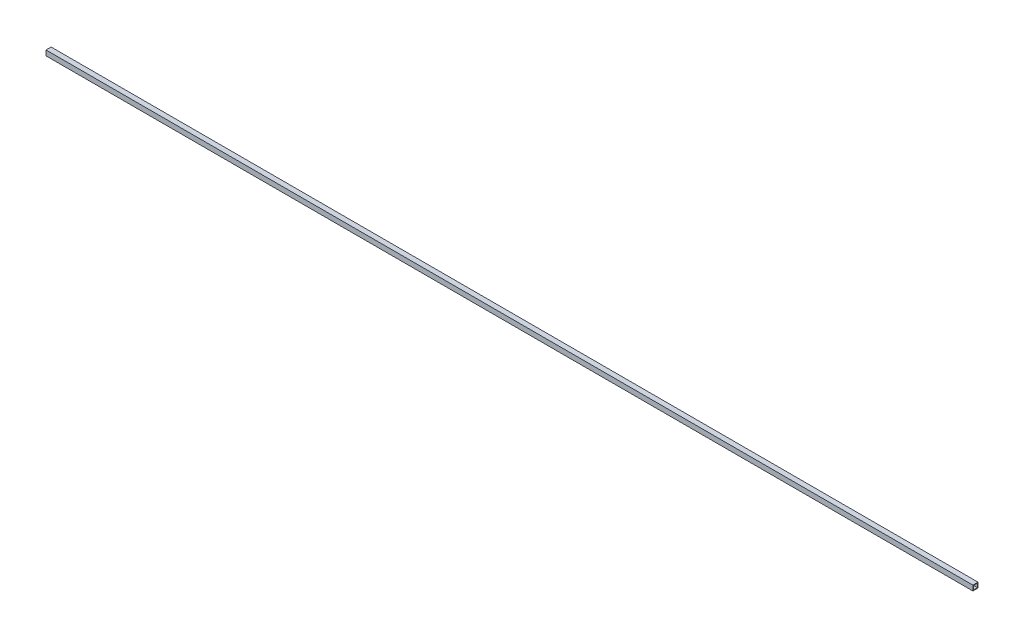
SolidWorks part; units mm, degrees
material "AISI 304"
ref_plane "Plan de face" through (0, 0, 0) normal (0, 0, 1) x (1, 0, 0)
ref_plane "Plan de dessus" through (0, 0, 0) normal (0, 1, 0) x (1, 0, 0)
ref_plane "Plan de droite" through (0, 0, 0) normal (1, 0, 0) x (0, 0, -1)
sketch "Sketch1" plane through (0, 0, 0) normal (0, 0, 1) x (1, 0, 0)
  line L0 (0, 0) -> (9193.53, 0)
  line L1 (3838.2575, 0) -> (-3838.2575, 0) construction
  dimension "D1" = 9193.53
other "Al tube square AL TUBE 2 SQR X 0.25 WALL(1)"
ref_plane "Plane1" through (0, 0, 0) normal (1, 0, 0) x (0, 1, 0)
sketch "Sketch11" plane through (0, 0, 0) normal (1, 0, 0) x (0, 1, 0)
  line L0 (-19.05, -19.05) -> (-19.05, 19.05)
  line L1 (19.05, 19.05) -> (-19.05, 19.05)
  line L2 (19.05, 19.05) -> (19.05, -19.05)
  line L3 (-19.05, -19.05) -> (19.05, -19.05)
  line L4 (-25.4, -25.4) -> (25.4, -25.4)
  line L5 (-25.4, -25.4) -> (-25.4, 25.4)
  line L6 (25.4, 25.4) -> (-25.4, 25.4)
  line L7 (25.4, 25.4) -> (25.4, -25.4)
  line L8 (0, -19.05) -> (0, -25.4) construction
  line L9 (0, -19.05) -> (0, 19.05) construction
  line L10 (0, 19.05) -> (0, 25.4) construction
  line L11 (25.4, 0) -> (19.05, 0) construction
  line L12 (19.05, 0) -> (-19.05, 0) construction
  line L13 (-19.05, 0) -> (-25.4, 0) construction
  point P14 (0, 0)
  point P17 (0, 0)
  dimension "Thickness" = 6.35
  dimension "V_leg" = 50.8
  dimension "H_leg" = 50.8
ref_plane "Midplane" through (4596.765, 0, 0) normal (-1, 0, 0) x (0, 0, 1)
